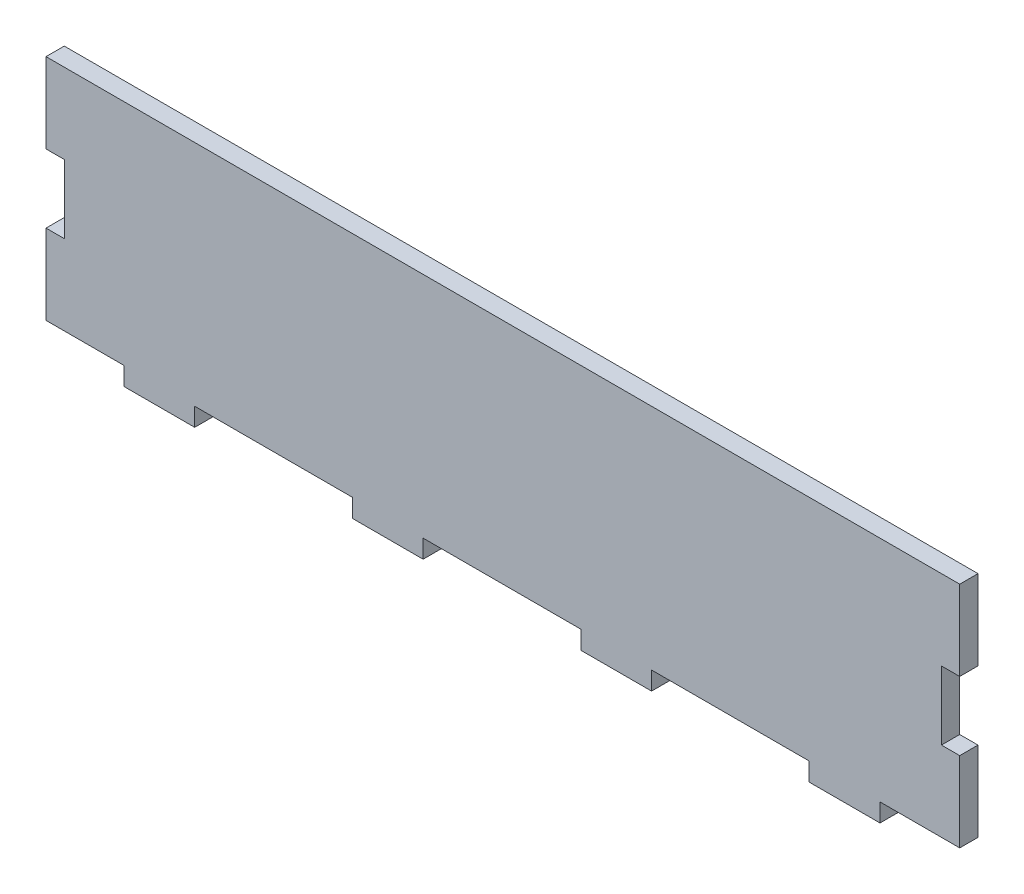
SolidWorks part; units mm, degrees
ref_plane "Ebene vorne" through (0, 0, 0) normal (0, 0, 1) x (1, 0, 0)
ref_plane "Ebene oben" through (0, 0, 0) normal (0, 1, 0) x (1, 0, 0)
ref_plane "Ebene rechts" through (0, 0, 0) normal (1, 0, 0) x (0, 0, -1)
sketch "Skizze1" plane through (0, 0, 0) normal (0, 0, 1) x (1, 0, 0)
  line L1 (0, 0) -> (200, 0)
  line L2 (0, 0) -> (0, 50)
  line L3 (0, 50) -> (200, 50)
  line L4 (200, 0) -> (200, 50)
  dimension "D1" = 200
  dimension "D2" = 50
extrude "Aufsatz-Linear austragen1" add sketch "Skizze1" along normal blind 4
sketch "Skizze2" plane through (0, 0, 4) normal (0, 0, -1) x (-1, 0, 0)
  line L0 (0, 0) -> (-200, 0) construction
  line L1 (-182.55, 0) -> (-167.05, 0)
  line L2 (-182.55, 0) -> (-182.55, -4)
  line L3 (-182.55, -4) -> (-167.05, -4)
  line L4 (-167.05, 0) -> (-167.05, -4)
  line L5 (-200, 0) -> (-200, 50) construction
  line L6 (-132.55, 0) -> (-117.05, 0)
  line L7 (-132.55, 0) -> (-132.55, -4)
  line L8 (-132.55, -4) -> (-117.05, -4)
  line L9 (-117.05, 0) -> (-117.05, -4)
  line L10 (-82.55, 0) -> (-67.05, 0)
  line L11 (-82.55, 0) -> (-82.55, -4)
  line L12 (-82.55, -4) -> (-67.05, -4)
  line L13 (-67.05, 0) -> (-67.05, -4)
  line L14 (-32.55, 0) -> (-17.05, 0)
  line L15 (-32.55, 0) -> (-32.55, -4)
  line L16 (-32.55, -4) -> (-17.05, -4)
  line L17 (-17.05, 0) -> (-17.05, -4)
  line L22 (17.45, 0) -> (32.95, 0) [skipped]
  line L23 (17.45, 0) -> (17.45, -4) [skipped]
  line L24 (17.45, -4) -> (32.95, -4) [skipped]
  line L25 (32.95, 0) -> (32.95, -4) [skipped]
  dimension "D1" = 15.5
  dimension "D2" = 17.45
  dimension "D3" = 4
  dimension "D4" = 5
extrude "Aufsatz-Linear austragen2" add sketch "Skizze2" along normal blind 4
sketch "Skizze4" plane through (0, 0, 4) normal (0, 0, 1) x (1, 0, 0)
  line L0 (0, 50) -> (0, 0) construction
  line L1 (0, 32.5) -> (4, 32.5)
  line L2 (0, 32.5) -> (0, 17.5)
  line L3 (0, 17.5) -> (4, 17.5)
  line L4 (4, 32.5) -> (4, 17.5)
  line L5 (200, 50) -> (0, 50) construction
  line L6 (100, 50) -> (100, -17.3733) construction
  line L7 (196, 32.5) -> (196, 17.5)
  line L8 (200, 17.5) -> (196, 17.5)
  line L9 (200, 32.5) -> (200, 17.5)
  line L10 (200, 32.5) -> (196, 32.5)
  dimension "D1" = 4
  dimension "D2" = 15
  dimension "D3" = 17.5
extrude "Schnitt-Linear austragen1" cut sketch "Skizze4" against normal up to next
